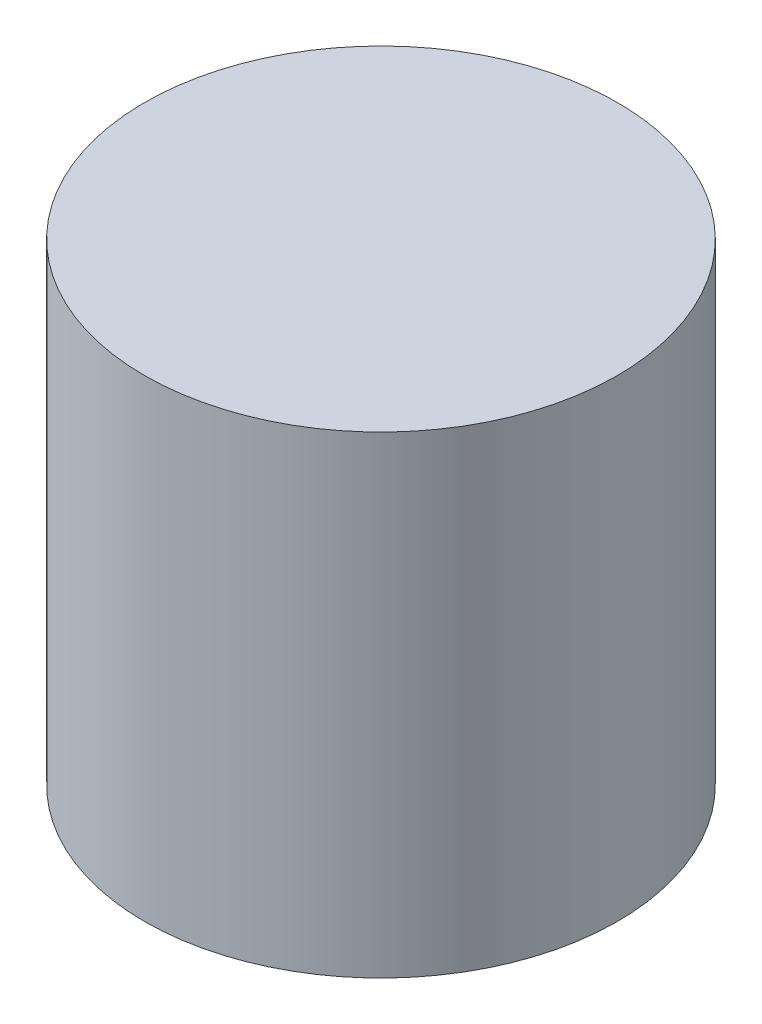
SolidWorks part; units mm, degrees
ref_plane "Front Plane" through (0, 0, 0) normal (0, 0, 1) x (1, 0, 0)
ref_plane "Top Plane" through (0, 0, 0) normal (0, 1, 0) x (1, 0, 0)
ref_plane "Right Plane" through (0, 0, 0) normal (1, 0, 0) x (0, 0, -1)
sketch "Sketch1" plane through (0, 0, 0) normal (0, 1, 0) x (1, 0, 0)
  circle A0 centre (0, 0) radius 1.5
  dimension "D1" = 3
extrude "Boss-Extrude1" add sketch "Sketch1" along normal blind 3
